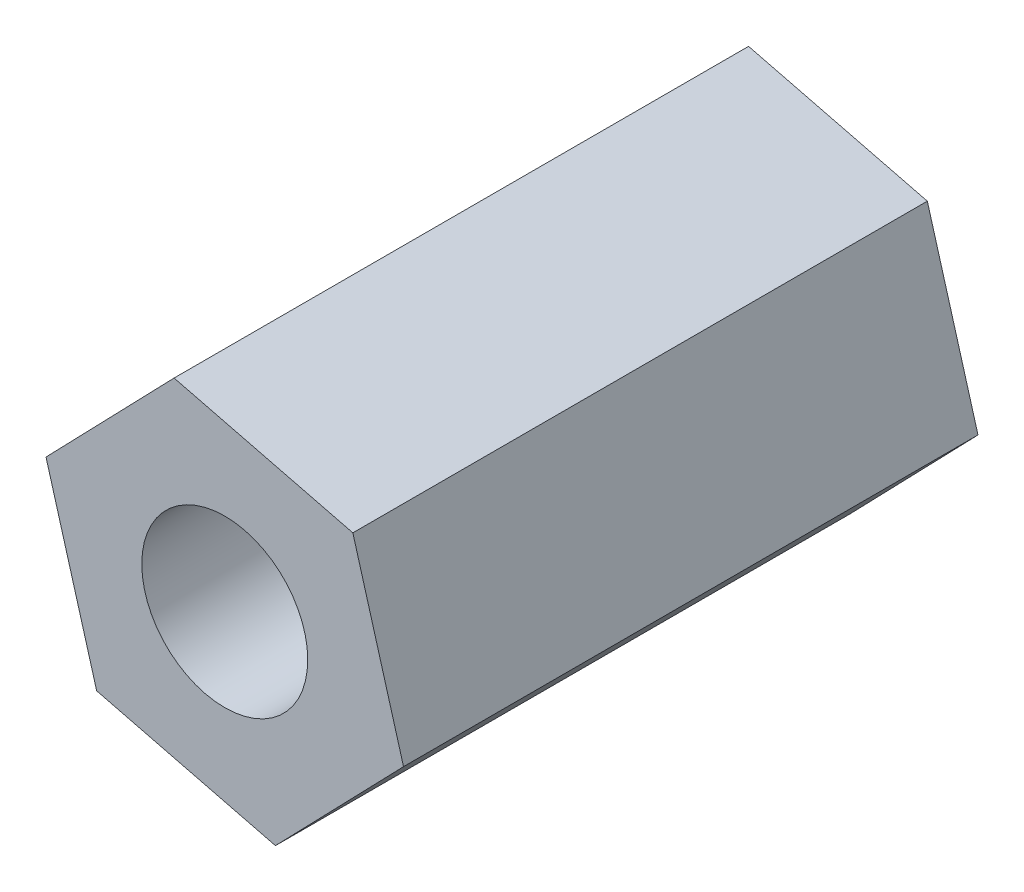
SolidWorks part; units mm, degrees
ref_plane "Front Plane" through (0, 0, 0) normal (0, 0, 1) x (1, 0, 0)
ref_plane "Top Plane" through (0, 0, 0) normal (0, 1, 0) x (1, 0, 0)
ref_plane "Right Plane" through (0, 0, 0) normal (1, 0, 0) x (0, 0, -1)
sketch "Sketch1" plane through (0, 0, 0) normal (0, 0, 1) x (1, 0, 0)
  line L1 (-7.1134, 1.7784) -> (-5.0968, -5.2712)
  line L2 (-5.0968, -5.2712) -> (2.0166, -7.0496)
  line L3 (2.0166, -7.0496) -> (7.1134, -1.7784)
  line L4 (7.1134, -1.7784) -> (5.0968, 5.2712)
  line L5 (5.0968, 5.2712) -> (-2.0166, 7.0496)
  line L6 (-2.0166, 7.0496) -> (-7.1134, 1.7784)
  circle A0 centre (0, 0) radius 6.35 construction
  dimension "D1" = 12.7
extrude "Boss-Extrude1" add sketch "Sketch1" along normal blind 22.86
sketch "Sketch2" plane through (0, 0, 0) normal (0, 0, -1) x (-1, 0, 0)
  circle A0 centre (0, 0) radius 3.302
  dimension "D1" = 6.604
extrude "Cut-Extrude1" cut sketch "Sketch2" against normal blind 39.878
